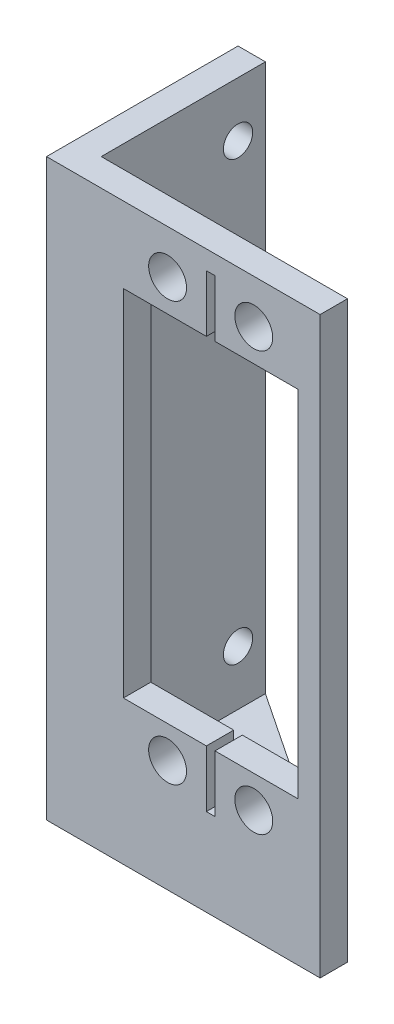
SolidWorks part; units mm, degrees
ref_plane "Front Plane" through (0, 0, 0) normal (0, 0, 1) x (1, 0, 0)
ref_plane "Top Plane" through (0, 0, 0) normal (0, 1, 0) x (1, 0, 0)
ref_plane "Right Plane" through (0, 0, 0) normal (1, 0, 0) x (0, 0, -1)
sketch "Sketch2" plane through (0, 0, 0) normal (0, 0, 1) x (1, 0, 0)
  line L1 (0, 0) -> (31.75, 0)
  line L2 (0, 0) -> (0, 63.5)
  line L3 (0, 63.5) -> (31.75, 63.5)
  line L4 (31.75, 0) -> (31.75, 63.5)
  dimension "D1" = 63.5
  dimension "D2" = 31.75
extrude "Boss-Extrude1" add sketch "Sketch2" along normal blind 3.175 contours L4 L3 L2 L1
sketch "Sketch3" plane through (0, 0, 3.175) normal (0, 0, 1) x (1, 0, 0)
  line L0 (8.923, 54.704) -> (29.177, 13.55) construction
  line L1 (8.923, 54.704) -> (18.55, 54.704)
  line L2 (8.923, 54.704) -> (8.923, 13.55)
  line L3 (8.923, 13.55) -> (18.55, 13.55)
  line L4 (29.177, 54.704) -> (29.177, 13.55)
  line L5 (29.177, 54.704) -> (8.923, 13.55) construction
  line L6 (14.05, 58.427) -> (24.05, 9.827) construction
  line L7 (14.05, 9.827) -> (24.05, 58.427) construction
  line L8 (19.55, 13.55) -> (29.177, 13.55)
  line L9 (18.55, 13.55) -> (18.55, 6.946)
  line L10 (18.55, 6.946) -> (19.55, 6.946)
  line L11 (19.55, 13.55) -> (19.55, 6.946)
  line L12 (19.05, 34.127) -> (62.1329, 34.127) construction
  line L13 (18.55, 61.308) -> (19.55, 61.308)
  line L14 (18.55, 54.704) -> (18.55, 61.308)
  line L15 (19.55, 54.704) -> (19.55, 61.308)
  line L16 (19.55, 54.704) -> (29.177, 54.704)
  line L17 (0, 0) -> (0, 63.5) construction
  line L18 (0, 63.5) -> (31.75, 63.5) construction
  circle A0 centre (14.05, 9.827) radius 2.2
  circle A1 centre (24.05, 9.827) radius 2.2
  circle A2 centre (14.05, 58.427) radius 2.2
  circle A3 centre (24.05, 58.427) radius 2.2
  point P8 (19.05, 6.946)
  point P17 (19.05, 34.127)
  point P18 (19.05, 34.127)
  point P27 (19.05, 44.45)
  dimension "D3" = 4.4
  dimension "D1" = 10
  dimension "D2" = 48.6
  dimension "D4" = 41.154
  dimension "D5" = 20.254
  dimension "D6" = 1
  dimension "D7" = 6.604
  dimension "D8" = 30.9
  dimension "D9" = 19.05
  dimension "D10" = 19.05
extrude "Cut-Extrude1" cut sketch "Sketch3" against normal through all
sketch "Sketch4" plane through (0, 0, 3.175) normal (0, 0, 1) x (1, 0, 0)
  line L0 (0, 0) -> (31.75, 0) construction
  line L1 (0, 63.5) -> (3.175, 63.5)
  line L2 (0, 63.5) -> (0, 0)
  line L3 (0, 0) -> (3.175, 0)
  line L4 (3.175, 63.5) -> (3.175, 0)
  dimension "D1" = 3.175
extrude "Boss-Extrude2" add sketch "Sketch4" against normal blind 19.05 from surface at -3.175 starting at face at (26.25, 9.827, 0)
sketch "Sketch5" plane through (0, 0, 0) normal (0, -1, 0) x (1, 0, 0)
  line L0 (0, 3.175) -> (31.75, 3.175)
  line L1 (31.75, 3.175) -> (31.75, 0)
  line L2 (31.75, 0) -> (3.175, -19.05)
  line L3 (3.175, -19.05) -> (0, -19.05)
  line L4 (0, -19.05) -> (0, 3.175)
extrude "Boss-Extrude3" add sketch "Sketch5" along normal blind 3.175
sketch "Sketch6" plane through (3.175, 0, 0) normal (1, 0, 0) x (0, 0, -1)
  line L0 (0, 0) -> (0, 63.5) construction
  line L1 (19.05, 0) -> (19.05, 63.5) construction
  line L2 (19.05, 63.5) -> (0, 63.5) construction
  line L4 (19.05, 0) -> (0, 0) construction
  circle A0 centre (3.175, 57.15) radius 1.7
  circle A1 centre (3.175, 6.35) radius 1.7
  circle A2 centre (15.875, 57.15) radius 1.7
  circle A3 centre (15.875, 6.35) radius 1.7
  dimension "D5" = 3.4
  dimension "D1" = 3.175
  dimension "D2" = 3.175
  dimension "D3" = 6.35
  dimension "D4" = 6.35
extrude "Cut-Extrude2" cut sketch "Sketch6" against normal through all
equation "\"D8@Sketch3\"=30.9mm"
equation "\"tighttol\" = 0.005in"
equation "\"normtol\" = 0.01in"
equation "\"loosetol\" = 0.02in"
equation "\"D5@Sketch6\"=3.4mm"
equation "\"D3@Sketch3\"=4.4mm"
